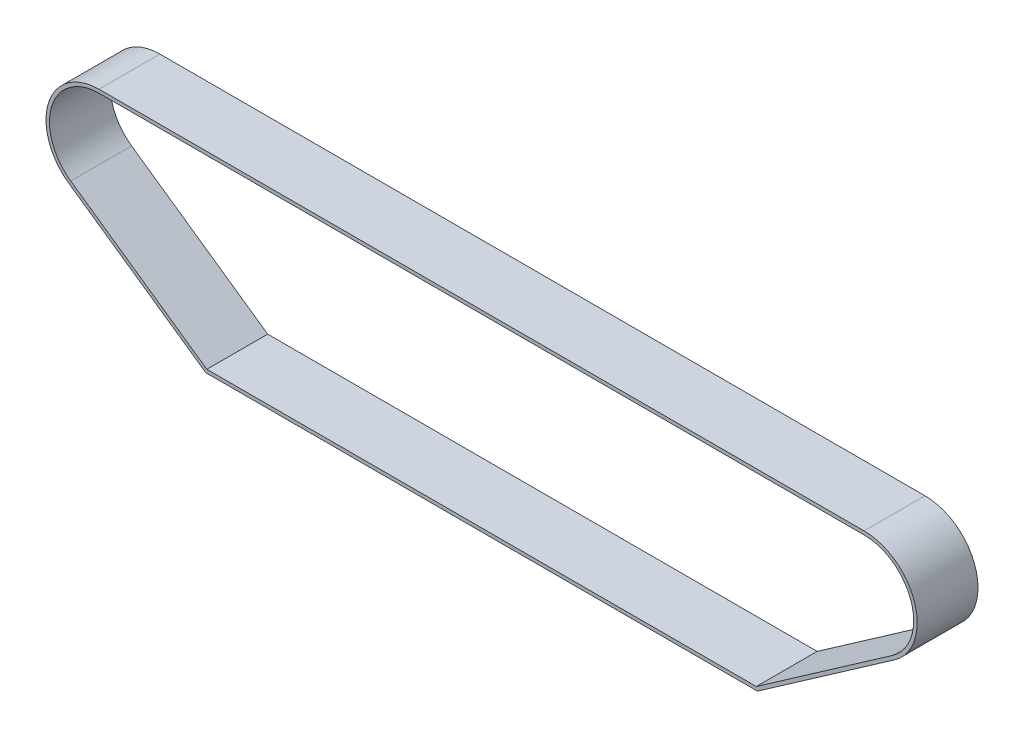
SolidWorks part; units mm, degrees
ref_plane "前视基准面" through (0, 0, 0) normal (0, 0, 1) x (1, 0, 0)
ref_plane "上视基准面" through (0, 0, 0) normal (0, 1, 0) x (1, 0, 0)
ref_plane "右视基准面" through (0, 0, 0) normal (1, 0, 0) x (0, 0, -1)
sketch "草图1" plane through (0, 0, 0) normal (0, 0, 1) x (1, 0, 0)
  line L0 (-220, 0) -> (220, 0) construction
  line L1 (-220, 28.5) -> (220, 28.5)
  line L2 (158, -78) -> (-158, -78)
  line L3 (-158, -78) -> (-236.3059, -23.3745)
  line L4 (158, -78) -> (236.3059, -23.3745)
  arc A0 (-220, 28.5) -> (-236.3059, -23.3745) centre (-220, 0) ccw
  arc A1 (236.3059, -23.3745) -> (220, 28.5) centre (220, 0) ccw
  point P4 (0, 0)
  dimension "D2" = 57
  dimension "D1" = 440
  dimension "D3" = 78
  dimension "D4" = 62
  dimension "D5" = 62
extrude "拉伸-薄壁1" add sketch "草图1" along normal blind 35 thin thin type one direction wall 2
